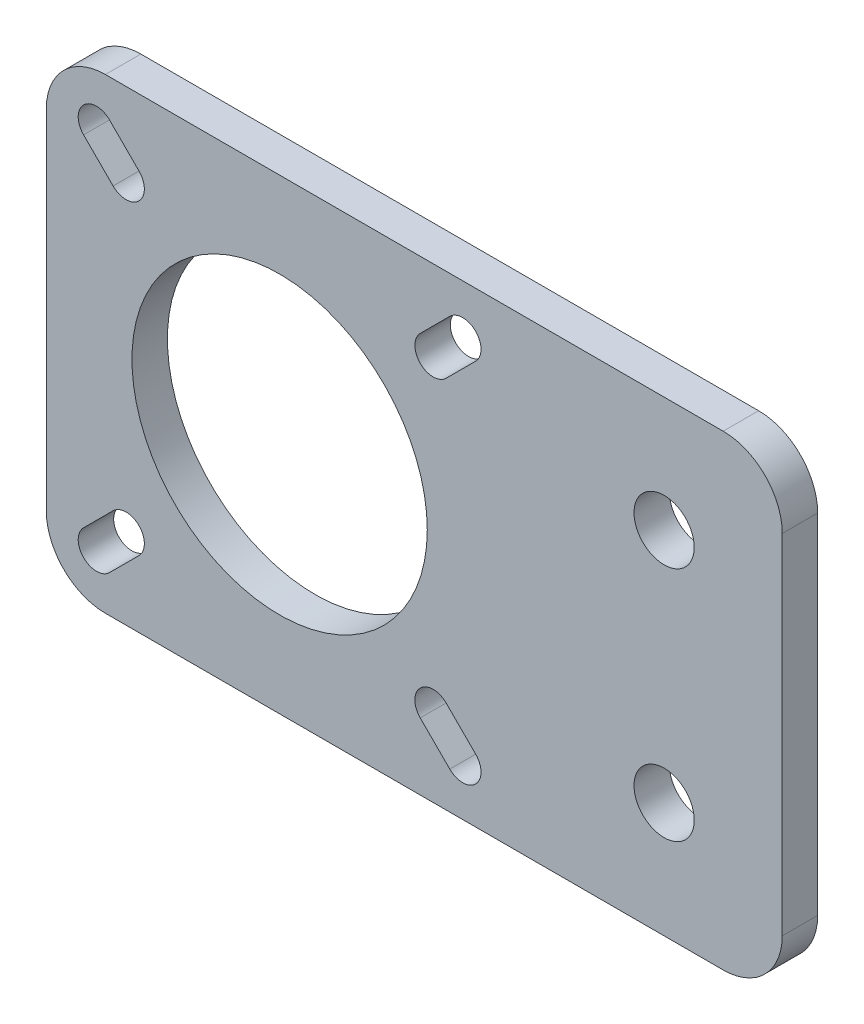
SolidWorks part; units mm, degrees
ref_plane "Front Plane" through (0, 0, 0) normal (0, 0, 1) x (1, 0, 0)
ref_plane "Top Plane" through (0, 0, 0) normal (0, 1, 0) x (1, 0, 0)
ref_plane "Right Plane" through (0, 0, 0) normal (1, 0, 0) x (0, 0, -1)
sketch "Sketch1" plane through (0, 0, 0) normal (0, 0, 1) x (1, 0, 0)
  line L0 (0, 39.5) -> (39.5, 0) construction
  line L1 (0, 0) -> (62.3, 0)
  line L2 (0, 0) -> (0, 39.5)
  line L3 (0, 39.5) -> (62.3, 39.5)
  line L5 (0, 0) -> (39.5, 39.5) construction
  line L6 (4.25, 35.25) -> (6.75, 32.75) construction
  line L7 (5.346, 36.346) -> (7.846, 33.846)
  line L8 (3.154, 34.154) -> (5.654, 31.654)
  line L9 (19.75, 39.5) -> (19.75, 0) construction
  line L10 (0, 19.75) -> (39.5, 19.75) construction
  line L11 (35.25, 35.25) -> (32.75, 32.75) construction
  line L12 (34.154, 36.346) -> (31.654, 33.846)
  line L13 (36.346, 34.154) -> (33.846, 31.654)
  line L14 (35.25, 4.25) -> (32.75, 6.75) construction
  line L15 (34.154, 3.154) -> (31.654, 5.654)
  line L16 (36.346, 5.346) -> (33.846, 7.846)
  line L17 (4.25, 4.25) -> (6.75, 6.75) construction
  line L18 (5.346, 3.154) -> (7.846, 5.654)
  line L19 (3.154, 5.346) -> (5.654, 7.846)
  line L20 (39.5, 39.5) -> (39.5, 0) construction
  line L21 (52.3, 39.5) -> (52.3, 0) construction
  line L22 (62.3, 39.5) -> (62.3, 0)
  circle A0 centre (19.75, 19.75) radius 12.5
  arc A1 (5.346, 36.346) -> (3.154, 34.154) centre (4.25, 35.25) ccw
  arc A2 (5.654, 31.654) -> (7.846, 33.846) centre (6.75, 32.75) ccw
  arc A3 (34.154, 36.346) -> (36.346, 34.154) centre (35.25, 35.25) cw
  arc A4 (33.846, 31.654) -> (31.654, 33.846) centre (32.75, 32.75) cw
  arc A5 (34.154, 3.154) -> (36.346, 5.346) centre (35.25, 4.25) ccw
  arc A6 (33.846, 7.846) -> (31.654, 5.654) centre (32.75, 6.75) ccw
  arc A7 (5.346, 3.154) -> (3.154, 5.346) centre (4.25, 4.25) cw
  arc A8 (5.654, 7.846) -> (7.846, 5.654) centre (6.75, 6.75) cw
  circle A9 centre (52.3, 19.75) radius 2.55 construction
  circle A10 centre (52.3, 29.75) radius 2.55
  circle A11 centre (52.3, 9.75) radius 2.55
  point P11 (5.5, 34)
  point P22 (34, 34)
  point P29 (34, 5.5)
  point P36 (5.5, 5.5)
  dimension "D5" = 25
  dimension "D8" = 35.25
  dimension "D9" = 5.1
  dimension "D2" = 39.5
  dimension "D3" = 45
  dimension "D4" = 45
  dimension "D6" = 3.1
  dimension "D7" = 32.75
  dimension "D10" = 32.55
  dimension "D11" = 10
  dimension "D12" = 10
  dimension "D13" = 10
extrude "Boss-Extrude1" add sketch "Sketch1" along normal blind 3
fillet "Fillet1" radius 5 4 edges at (0, 0, 1.5) (0, 39.5, 1.5) (62.3, 0, 1.5) (62.3, 39.5, 1.5)
